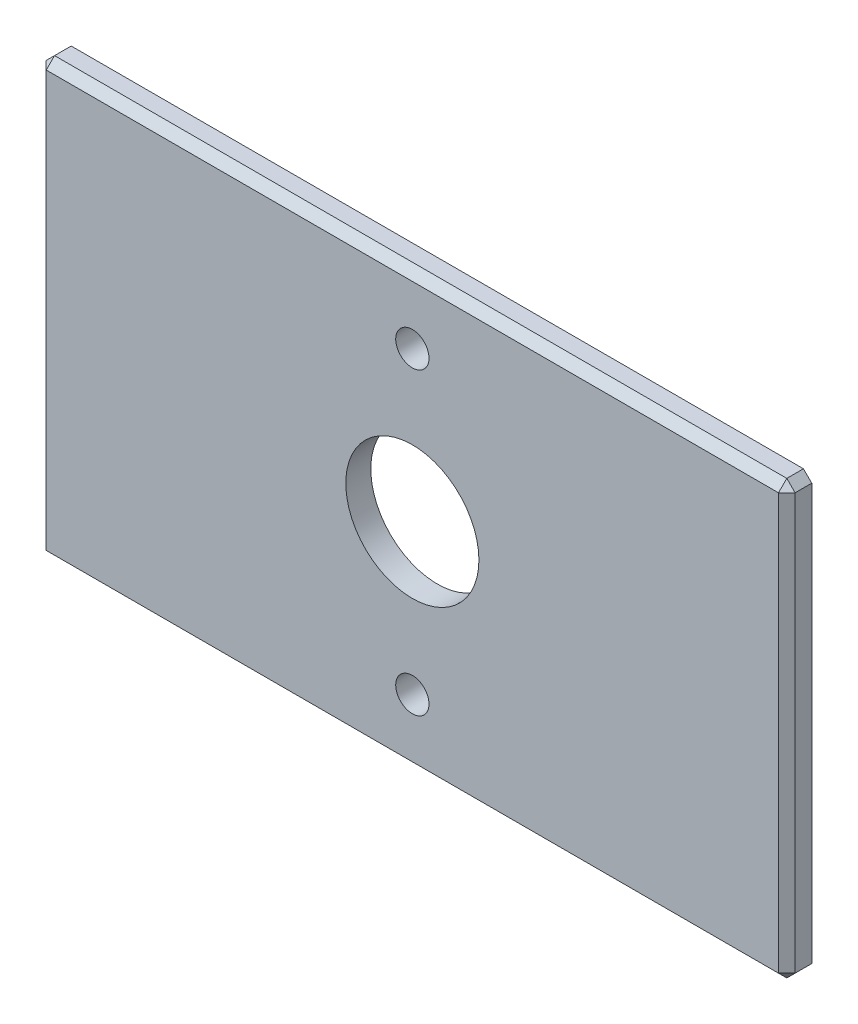
SolidWorks part; units mm, degrees
material "PLA"
ref_plane "Front Plane" through (0, 0, 0) normal (0, 0, 1) x (1, 0, 0)
ref_plane "Top Plane" through (0, 0, 0) normal (0, 1, 0) x (1, 0, 0)
ref_plane "Right Plane" through (0, 0, 0) normal (1, 0, 0) x (0, 0, -1)
sketch "Sketch1" plane through (0, 0, 0) normal (0, 0, 1) x (1, 0, 0)
  line L1 (-22.5, -13) -> (22.5, -13)
  line L2 (-22.5, -13) -> (-22.5, 13)
  line L3 (-22.5, 13) -> (22.5, 13)
  line L4 (22.5, -13) -> (22.5, 13)
  line L5 (-22.5, -13) -> (22.5, 13) construction
  line L6 (-22.5, 13) -> (22.5, -13) construction
  circle A0 centre (0, 0) radius 4
  circle A1 centre (0, 9) radius 1
  circle A2 centre (0, -9) radius 1
  point P0 (0, 0)
  dimension "D3" = 8
  dimension "D4" = 2
  dimension "D6" = 2
  dimension "D1" = 26
  dimension "D2" = 45
  dimension "D5" = 9
  dimension "D7" = 9
extrude "Boss-Extrude1" add sketch "Sketch1" along normal mid plane 1.5
chamfer "Chamfer1" distance 0.5 angle 45 8 edges at (0, -13, 0.75) (22.5, 0, 0.75) (-22.5, 0, 0.75) (0, 13, 0.75) (-22.5, -13, 0) (22.5, -13, 0) (22.5, 13, 0) (-22.5, 13, 0)
